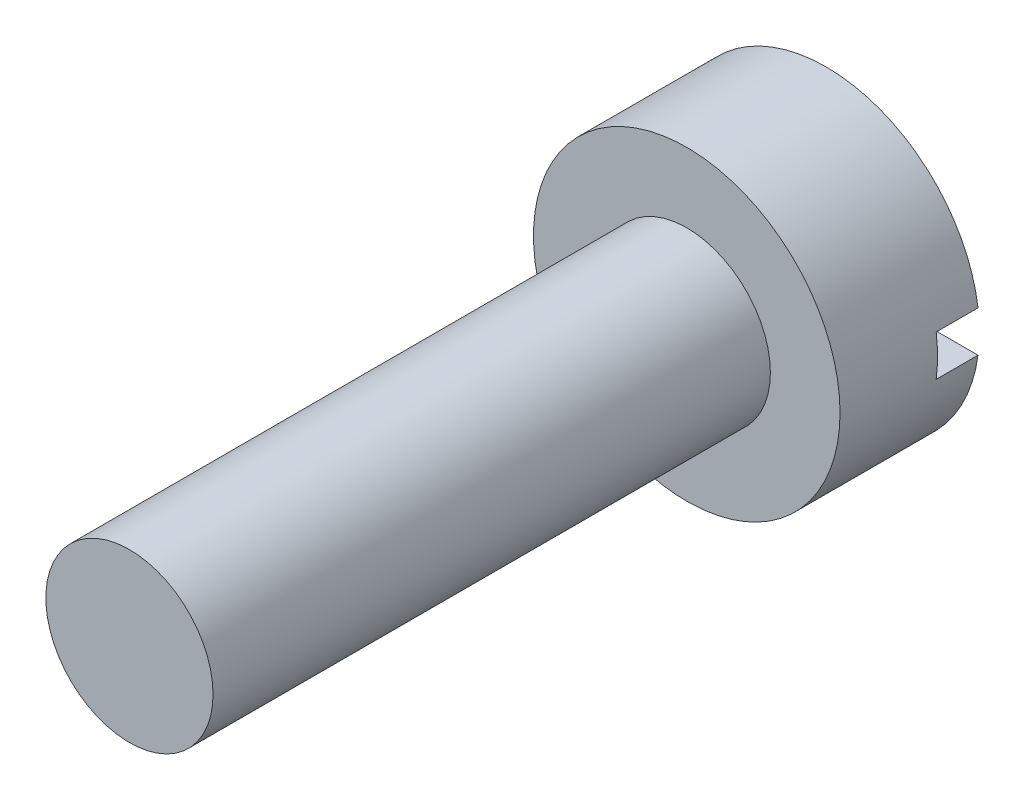
SolidWorks part; units mm, degrees
material "1.5714 (16NiCr4)"
ref_plane "Plan de face" through (0, 0, 0) normal (0, 0, 1) x (1, 0, 0)
ref_plane "Plan de dessus" through (0, 0, 0) normal (0, 1, 0) x (1, 0, 0)
ref_plane "Plan de droite" through (0, 0, 0) normal (1, 0, 0) x (0, 0, -1)
sketch "Esquisse1" plane through (0, 0, 0) normal (0, 0, 1) x (1, 0, 0)
  circle A0 centre (0, 0) radius 2.75
  dimension "D1" = 5.5
extrude "Boss.-Extru.1" add sketch "Esquisse1" along normal blind 2.5
sketch "Esquisse2" plane through (0, 0, 2.5) normal (0, 0, 1) x (1, 0, 0)
  circle A0 centre (0, 0) radius 1.5
  dimension "D1" = 3
extrude "Boss.-Extru.2" add sketch "Esquisse2" along normal blind 10
sketch "Esquisse3" plane through (0, 0, 0) normal (0, 0, -1) x (-1, 0, 0)
  line L1 (-3.6933, -0.3675) -> (3.6933, -0.3675)
  line L2 (-3.6933, -0.3675) -> (-3.6933, 0.3675)
  line L3 (-3.6933, 0.3675) -> (3.6933, 0.3675)
  line L4 (3.6933, -0.3675) -> (3.6933, 0.3675)
  line L5 (-3.6933, -0.3675) -> (3.6933, 0.3675) construction
  line L6 (-3.6933, 0.3675) -> (3.6933, -0.3675) construction
  point P0 (0, 0)
extrude "Enlèv. mat.-Extru.1" cut sketch "Esquisse3" against normal blind 0.75
